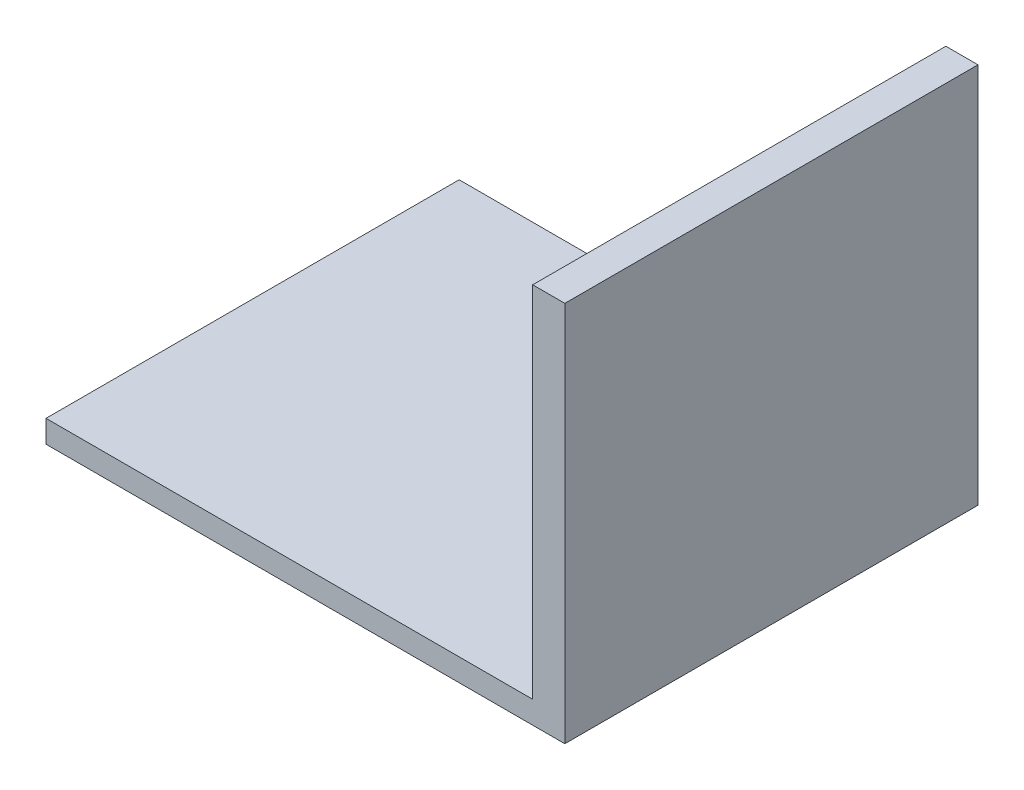
SolidWorks part; units mm, degrees
ref_plane "Front Plane" through (0, 0, 0) normal (0, 0, 1) x (1, 0, 0)
ref_plane "Top Plane" through (0, 0, 0) normal (0, 1, 0) x (1, 0, 0)
ref_plane "Right Plane" through (0, 0, 0) normal (1, 0, 0) x (0, 0, -1)
sketch "Sketch1" plane through (0, 0, 0) normal (0, 1, 0) x (1, 0, 0)
  line L1 (-40.3324, 34.6721) -> (52.1632, 34.6721)
  line L2 (-40.3324, 34.6721) -> (-40.3324, -38.9879)
  line L3 (-40.3324, -38.9879) -> (52.1632, -38.9879)
  line L4 (52.1632, 34.6721) -> (52.1632, -38.9879)
extrude "Boss-Extrude1" add sketch "Sketch1" along normal blind 4
sketch "Sketch2" plane through (0, 4, 0) normal (0, 1, 0) x (1, 0, 0)
  line L0 (-40.3324, -38.9879) -> (52.1632, -38.9879) construction
  line L1 (52.1632, 34.6721) -> (46.4344, 34.6721)
  line L2 (52.1632, 34.6721) -> (52.1632, -38.9879)
  line L3 (52.1632, -38.9879) -> (46.4344, -38.9879)
  line L4 (46.4344, 34.6721) -> (46.4344, -38.9879)
extrude "Boss-Extrude2" add sketch "Sketch2" along normal blind 64
